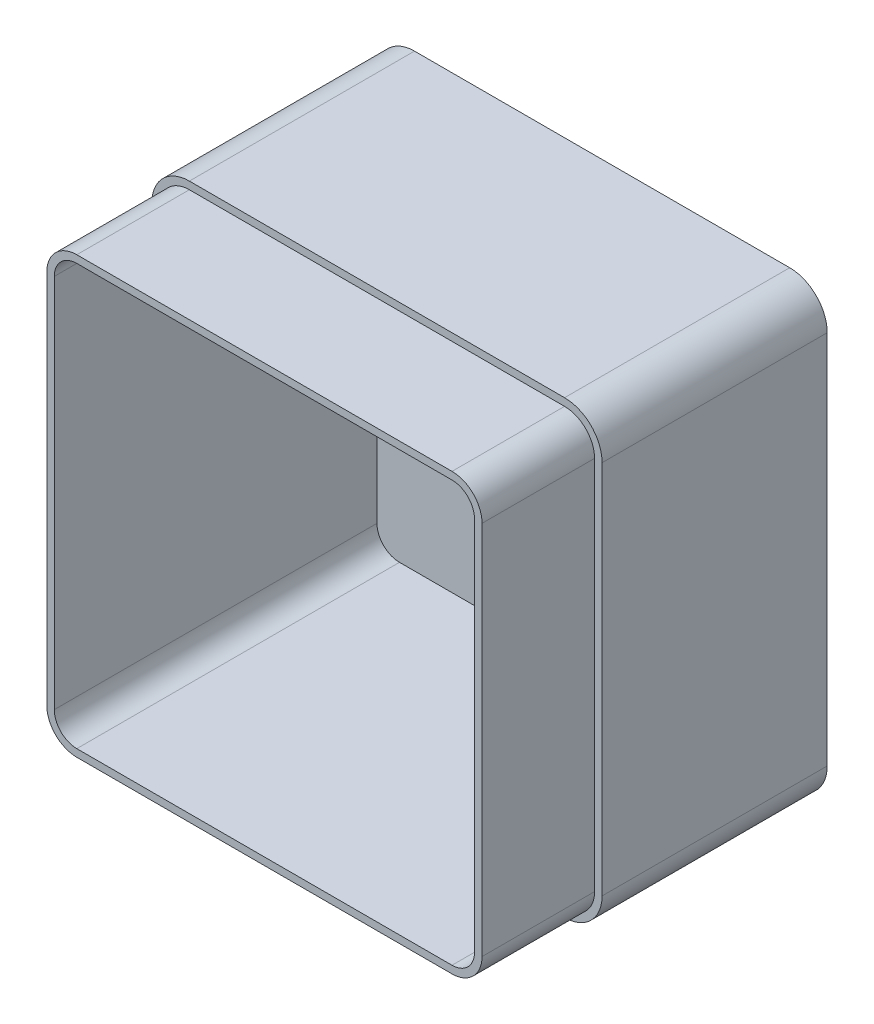
SolidWorks part; units mm, degrees
ref_plane "Přední rovina" through (0, 0, 0) normal (0, 0, 1) x (1, 0, 0)
ref_plane "Horní rovina" through (0, 0, 0) normal (0, 1, 0) x (1, 0, 0)
ref_plane "Pravá rovina" through (0, 0, 0) normal (1, 0, 0) x (0, 0, -1)
sketch "Skica1" plane through (0, 0, 0) normal (0, 0, 1) x (1, 0, 0)
  line L1 (0, 0) -> (120, 0)
  line L2 (0, 0) -> (0, 120)
  line L3 (0, 120) -> (120, 120)
  line L4 (120, 0) -> (120, 120)
  dimension "D1" = 120
  dimension "D2" = 120
extrude "Vysunout1" add sketch "Skica1" along normal blind 90
fillet "Zaoblit1" radius 10 1 edges at (120, 120, 45)
fillet "Zaoblit2" radius 10 1 edges at (0, 120, 45)
fillet "Zaoblit3" radius 10 1 edges at (0, 0, 45)
fillet "Zaoblit4" radius 10 1 edges at (120, 0, 45)
shell "Skořepina4" thickness 4
sketch "Skica2" plane through (0, 0, 90) normal (0, 0, 1) x (1, 0, 0)
  line L8 (10, 2) -> (110, 2)
  line L9 (118, 10) -> (118, 110)
  line L10 (110, 118) -> (10, 118)
  line L11 (2, 110) -> (2, 10)
  line L12 (10, 2) -> (110, 2)
  line L13 (118, 10) -> (118, 110)
  line L14 (110, 118) -> (10, 118)
  line L15 (2, 110) -> (2, 10)
  arc A8 (110, 2) -> (118, 10) centre (110, 10) ccw
  arc A9 (118, 110) -> (110, 118) centre (110, 110) ccw
  arc A10 (10, 118) -> (2, 110) centre (10, 110) ccw
  arc A11 (2, 10) -> (10, 2) centre (10, 10) ccw
  arc A12 (110, 2) -> (118, 10) centre (110, 10) ccw
  arc A13 (118, 110) -> (110, 118) centre (110, 110) ccw
  arc A14 (10, 118) -> (2, 110) centre (10, 110) ccw
  arc A15 (2, 10) -> (10, 2) centre (10, 10) ccw
  dimension "D1" = 2
extrude "Odebrat vysunutím1" cut sketch "Skica2" against normal blind 30 flip side to cut
